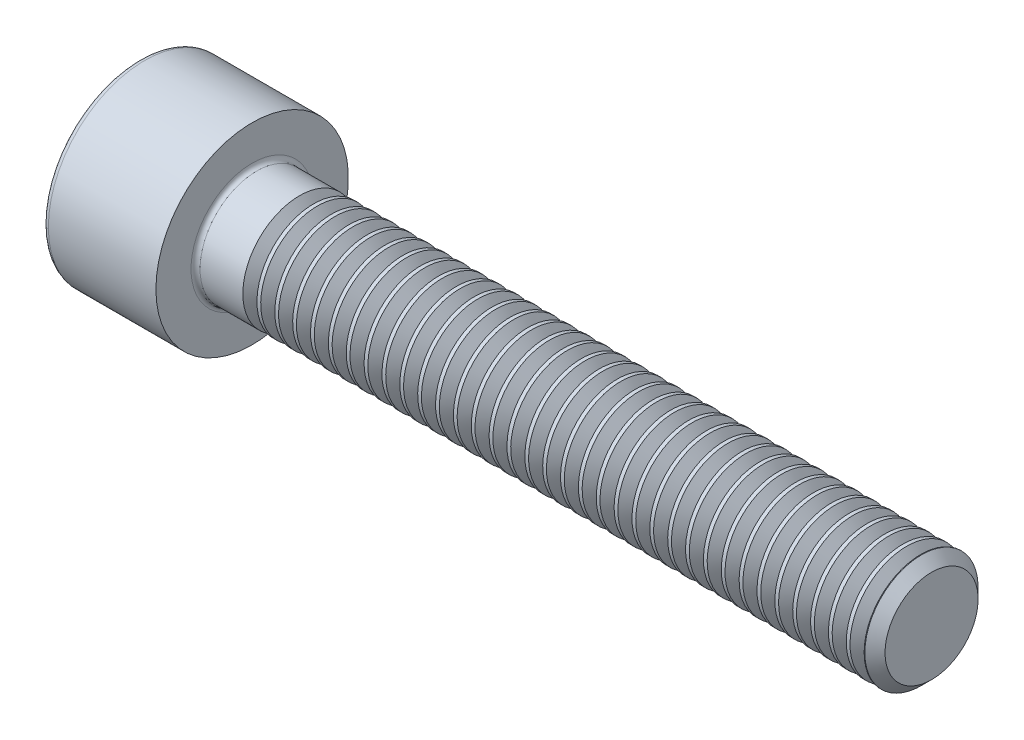
SolidWorks part; units mm, degrees
revolve "Base-Revolve" add sketch "BodySke"
sketch "BodySke" plane through (0, 0, 0) normal (0, 0, 1) x (1, 0, 0)
  line L0 (0, 0) -> (0, 4.25)
  line L1 (0, 4.25) -> (5, 4.25)
  line L2 (5, 4.25) -> (5, 2.5)
  line L3 (5, 2.5) -> (34.555, 2.5)
  line L4 (35, 2.055) -> (35, 0)
  line L5 (35, 0) -> (0, 0)
  line L6 (-31.75, 0) -> (127, 0) construction
  line L8 (35, 2.055) -> (34.555, 2.5)
  line L10 (35, -2.055) -> (34.555, -2.5) construction
  line L11 (5.8, 9.525) -> (5.8, 3.175) construction
  line L12 (5, 9.525) -> (5, 3.175) construction
  line L13 (-25, 9.525) -> (-25, 3.175) construction
  dimension "Head_ht" = 5
  dimension "Length" = 30
  dimension "Body_ch_ang" = 45
  dimension "Diameter" = 5
  dimension "Minor_dia" = 4.11
  dimension "Advance" = 0.8
  dimension "Thread_nom" = 30
  dimension "Thread_length" = 60
  dimension "Head_dia" = 8.5
cosmetic thread "ThreadCosmetic" [suppressed]
fillet "Fillet1" radius 0.2 1 edges at (5, 0, 2.5)
fillet "Fillet2" radius 0.25 1 edges at (0, 0, 4.25)
ref_plane "Plane1" through (0, 0, 0) normal (0, 0, 1) x (1, 0, 0)
ref_plane "Plane2" through (0, 0, 0) normal (0, 1, 0) x (1, 0, 0)
ref_plane "Plane3" through (0, 0, 0) normal (1, 0, 0) x (0, 0, -1)
sketch "Sketch2" plane through (0, 0, 0) normal (0, 0, 1) x (1, 0, 0)
  line L0 (0, 2.042) -> (2.5, 2.042)
  line L1 (2.5, 2.042) -> (3.6789, 0)
  line L2 (-31.75, 0) -> (127, 0) construction
  line L3 (3.6789, 0) -> (0, 0)
  line L4 (0, 0) -> (0, 2.042)
  line L6 (0, 0) -> (47.625, 0) construction
  dimension "D1" = 2.042
  dimension "D2" = 60
  dimension "Depth" = 2.5
revolve "Hex-PreBroach" cut sketch "Sketch2" angle 360 about L6
sketch "Sketch3" plane through (0, 0, 0) normal (-1, 0, 0) x (0, 0.5, 0.866)
  line L0 (1.1789, 2.042) -> (-1.1789, 2.042)
  line L1 (-1.1789, 2.042) -> (-2.3579, 0)
  line L2 (1.1789, 2.042) -> (2.3579, 0)
  line L3 (1.1789, -2.042) -> (2.3579, 0)
  line L4 (1.1789, -2.042) -> (-1.1789, -2.042)
  line L5 (-1.1789, -2.042) -> (-2.3579, 0)
  dimension "D1" = 2.042
  dimension "D2" = 2.042
  dimension "Hex_size" = 4.084
extrude "Hex" cut sketch "Sketch3" against normal blind 2.5
sketch "ThdSchSke" plane through (0, 0, 0) normal (0, 0, 1) x (1, 0, 0)
  line L0 (7.4, -2.055) -> (7.0884, -2.5)
  line L1 (7.4, -2.055) -> (7.7116, -2.5)
  line L2 (7.7116, -2.5) -> (7.7116, -3.125)
  line L3 (-3.175, 0) -> (5.1513, 0) construction
  line L4 (0, 4) -> (0, -4) construction
  line L5 (7.7116, -3.125) -> (7.0884, -3.125)
  line L6 (7.0884, -3.125) -> (7.0884, -2.5)
  dimension "Thread_minor" = 4.11
  dimension "Diameter" = 5
  dimension "Start" = 7.4
revolve "ThreadSchematic" cut sketch "ThdSchSke" angle 360 about L3
pattern_linear "ThdSchPat" count 35 spacing 0.7886 along (1, 0, 0) of "ThreadSchematic"
equation "\"D2@Sketch3\" = \"Hex_size@Sketch3\" / 2"
equation "\"D1@Sketch3\" = \"Hex_size@Sketch3\" / 2"
equation "\"D1@Sketch2\" = \"Hex_size@Sketch3\" / 2"
equation "\"Thread_minor@ThreadCosmetic\"  =  \"Minor_dia@BodySke\""
equation "\"Depth@Sketch2\" =  \"Key_eng@Hex\""
equation "\"Thread_length@ThreadCosmetic\" = ((sgn( (\"Length@BodySke\" - \"Advance@BodySke\" * 3.0) - \"Thread_nom@BodySke\" )-1)*( (\"Length@BodySke\" - \"Advance@BodySke\" * 3.0) - \"Thread_nom@BodySke\" ))/-2+ \"Thread_nom@BodySke\""
equation "\"Thread_minor@ThdSchSke\" = \"Minor_dia@BodySke\""
equation "\"Diameter@ThdSchSke\" = \"Diameter@BodySke\""
equation "\"Overcut@ThdSchSke\" = \"Diameter@BodySke\" * 1.25"
equation "\"Start@ThdSchSke\" = \"Head_ht@BodySke\" + \"Length@BodySke\" - \"Thread_length@ThreadCosmetic\"  '---Non-countersunk---"
equation "\"Num_threads@ThdSchPat\" = int( \"Thread_length@ThreadCosmetic\" / \"Advance@BodySke\" + 0.999 )  + 1"
equation "\"Advance@ThdSchPat\" = \"Thread_length@ThreadCosmetic\" /  (\"Num_threads@ThdSchPat\" - 1) 'relax it"
equation "\"Num_threads@ThdSchPat\" = \"Num_threads@ThdSchPat\" - sgn( \"Num_threads@ThdSchPat\" - 1) '---chamfered tips only---"
